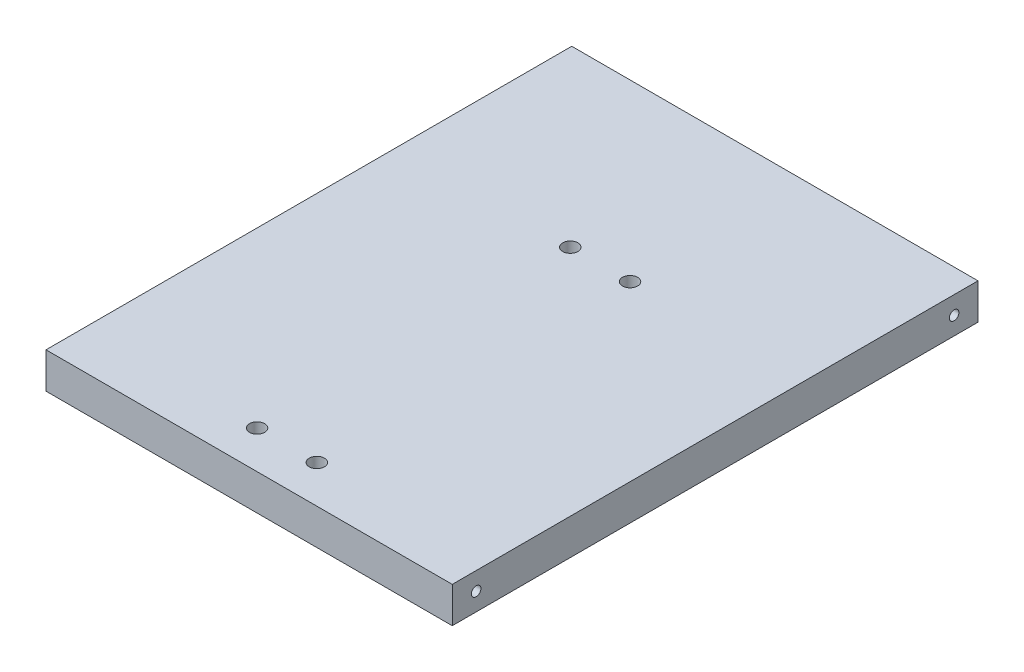
SolidWorks part; units mm, degrees
ref_plane "Front Plane" through (0, 0, 0) normal (0, 0, 1) x (1, 0, 0)
ref_plane "Top Plane" through (0, 0, 0) normal (0, 1, 0) x (1, 0, 0)
ref_plane "Right Plane" through (0, 0, 0) normal (1, 0, 0) x (0, 0, -1)
sketch "Sketch1" plane through (0, 0, 0) normal (0, 1, 0) x (1, 0, 0)
  line L1 (0, 0) -> (170, 0)
  line L2 (0, 0) -> (0, 220)
  line L3 (0, 220) -> (170, 220)
  line L4 (170, 0) -> (170, 220)
  dimension "D1" = 220
  dimension "D2" = 170
extrude "Boss-Extrude1" add sketch "Sketch1" along normal blind 15
sketch "Sketch2" plane through (0, 0, 0) normal (-1, 0, 0) x (0, 0, 1)
  line L0 (0, 7.5) -> (-220, 7.5) construction
  line L1 (0, 15) -> (0, 0) construction
  line L2 (-220, 15) -> (-220, 0) construction
  circle A0 centre (-10, 7.5) radius 2
  circle A1 centre (-210, 7.5) radius 2
  dimension "D1" = 4
  dimension "D4" = 4
  dimension "D2" = 10
  dimension "D3" = 200
sketch "Sketch3" plane through (0, 15, 0) normal (0, 1, 0) x (1, 0, 0)
  line L0 (85, 220) -> (85, 0) construction
  line L1 (170, 220) -> (0, 220) construction
  line L2 (0, 0) -> (170, 0) construction
  circle A0 centre (72.5, 15.8212) radius 3.175
  circle A1 centre (72.5, 146.8912) radius 3.175
  dimension "D3" = 6.35
  dimension "D4" = 6.35
  dimension "D1" = 131.07
  dimension "D2" = 12.5
  dimension "D5" = 12.5
extrude "Cut-Extrude1" cut sketch "Sketch2" against normal blind 20
extrude "Cut-Extrude2" cut sketch "Sketch3" against normal up to surface (15 mm away) up to face at (85, 0, -110)
ref_plane "Plane1" through (85, 0, 0) normal (-1, 0, 0) x (0, 0, 1)
mirror "Mirror1" about plane through (85, 0, 0) normal (-1, 0, 0) of "Cut-Extrude2", "Cut-Extrude1"
